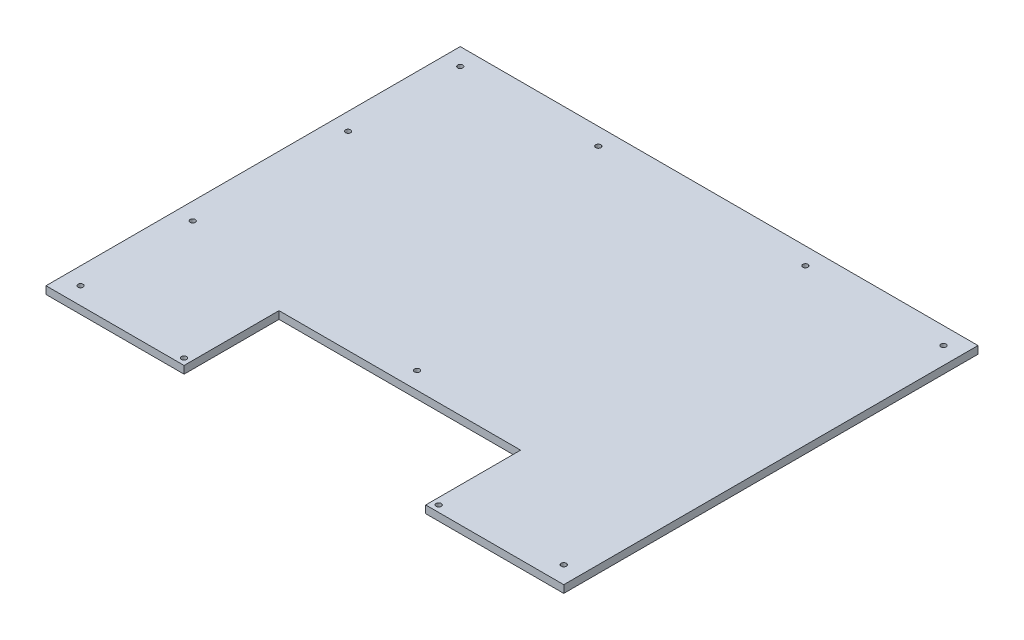
SolidWorks part; units mm, degrees
material "Polycarbonate"
ref_plane "Front Plane" through (0, 0, 0) normal (0, 0, 1) x (1, 0, 0)
ref_plane "Top Plane" through (0, 0, 0) normal (0, 1, 0) x (1, 0, 0)
ref_plane "Right Plane" through (0, 0, 0) normal (1, 0, 0) x (0, 0, -1)
sketch "Sketch1" plane through (0, 0, 0) normal (0, 1, 0) x (1, 0, 0)
  line L0 (0, 0) -> (0, -152.4) construction
  line L1 (-190.5, -152.4) -> (-88.9, -152.4)
  line L2 (-190.5, -152.4) -> (-190.5, 152.4)
  line L3 (-190.5, 152.4) -> (190.5, 152.4)
  line L4 (190.5, -152.4) -> (190.5, 152.4)
  line L5 (-190.5, -152.4) -> (190.5, 152.4) construction
  line L6 (-190.5, 152.4) -> (190.5, -152.4) construction
  line L8 (-88.9, -152.4) -> (-88.9, -82.55)
  line L9 (-88.9, -82.55) -> (88.9, -82.55)
  line L10 (88.9, -152.4) -> (88.9, -82.55)
  line L11 (88.9, -152.4) -> (190.5, -152.4)
  point P0 (0, 0)
  dimension "D1" = 304.8
  dimension "D2" = 381
  dimension "D3" = 69.85
  dimension "D4" = 177.8
extrude "Boss-Extrude1" add sketch "Sketch1" along normal blind 5.588
sketch "Sketch2" plane through (0, 5.588, 0) normal (0, 1, 0) x (1, 0, 0)
  line L0 (-177.8, 152.4) -> (-177.8, -152.4) construction
  line L1 (190.5, 152.4) -> (-190.5, 152.4) construction
  line L2 (-190.5, -152.4) -> (-88.9, -152.4) construction
  line L3 (-190.5, -139.7) -> (190.5, -139.7) construction
  line L4 (-190.5, 152.4) -> (-190.5, -152.4) construction
  line L5 (190.5, -152.4) -> (190.5, 152.4) construction
  line L6 (-190.5, 139.7) -> (190.5, 139.7) construction
  line L7 (177.8, 152.4) -> (177.8, -152.4) construction
  line L8 (-101.6, -152.4) -> (-101.6, -69.85) construction
  line L9 (-190.5, -152.4) -> (-88.9, -152.4) construction
  line L10 (-101.6, -69.85) -> (101.6, -69.85) construction
  line L11 (101.6, -69.85) -> (101.6, -152.4) construction
  line L12 (88.9, -152.4) -> (190.5, -152.4) construction
  line L13 (-88.9, -152.4) -> (-88.9, -82.55) construction
  line L14 (88.9, -82.55) -> (88.9, -152.4) construction
  line L15 (-88.9, -82.55) -> (88.9, -82.55) construction
  line L16 (177.8, 0) -> (-177.8, 0) construction
  line L17 (0, 139.7) -> (0, 0) construction
  line L18 (-93.6752, -139.7) -> (-93.6752, -147.6248) construction
  line L19 (-93.6752, -147.6248) -> (-101.6, -147.6248) construction
  line L20 (93.6752, -139.7) -> (93.6752, -147.6248) construction
  line L21 (93.6752, -147.6248) -> (101.6, -147.6248) construction
  point P20 (-177.8, -57.15)
  point P21 (-177.8, 57.15)
  point P22 (-76.2, 139.7)
  point P24 (76.2, 139.7)
  point P27 (-93.6752, -147.6248)
  point P38 (-88.9, -117.475)
  point P43 (0, -69.85)
  point P44 (-177.8, 139.7)
  point P45 (177.8, 139.7)
  point P46 (177.8, -139.7)
  point P47 (101.6, -139.7)
  point P48 (-101.6, -139.7)
  point P49 (-177.8, -139.7)
  point P56 (93.6752, -147.6248)
  dimension "D1" = 12.7
  dimension "D2" = 12.7
  dimension "D3" = 12.7
  dimension "D4" = 12.7
  dimension "D9" = 12.7
  dimension "D10" = 12.7
  dimension "D11" = 12.7
  dimension "D8" = 114.3
  dimension "D7" = 152.4
  dimension "D5" = 4.7752
  dimension "D6" = 4.7752
  dimension "D12" = 4.7752
hole_wizard "#6 Clearance Hole1" positions "3DSketch1" profile "Sketch3" hole size "#6" standard "ANSI Inch" end condition through all
sketch3d "3DSketch1"
  point P13 (-76.2, 5.588, -139.7)
  point P19 (76.2, 5.588, -139.7)
  point P43 (0, 5.588, 69.85)
  point P49 (-93.6752, 5.588, 147.6248)
  point P52 (-177.8, 5.588, 139.7)
  point P55 (-177.8, 5.588, -139.7)
  point P58 (177.8, 5.588, -139.7)
  point P61 (177.8, 5.588, 139.7)
  point P64 (93.6752, 5.588, 147.6248)
  point P74 (-177.8, 5.588, -57.15)
  point P77 (-177.8, 5.588, 57.15)
sketch "Sketch3" plane through (-76.2, 5.588, -139.7) normal (1, 0, 0) x (0, 0, 1)
  line L0 (0, 0) -> (0, 5.588)
  line L1 (0, 5.588) -> (1.8986, 5.588)
  line L2 (1.8986, 5.588) -> (1.8986, 0)
  line L5 (1.8986, 0) -> (0, 0)
  line L11 (0, -6.35) -> (0, 107.95) construction
  dimension "Thru Hole Dia." = 3.7973
  dimension "Thru Hole Depth" = 5.588
sketch "Sketch4" [suppressed] plane through (0, 3.175, 0) normal (0, 1, 0) x (1, 0, 0)
  line L1 (-114.3, -50.8) -> (-12.7, -50.8) construction
  line L2 (-114.3, -50.8) -> (-114.3, 25.4) construction
  line L3 (-114.3, 25.4) -> (-12.7, 25.4) construction
  line L4 (-12.7, -50.8) -> (-12.7, 25.4) construction
  line L5 (-190.5, 165.1) -> (-190.5, -165.1) construction
  line L6 (-88.9, -95.25) -> (88.9, -95.25) construction
  dimension "D1" = 76.2
  dimension "D2" = 44.45
  dimension "D3" = 101.6
  dimension "D4" = 76.2
hole_wizard "#6 Clearance Hole2" [suppressed] positions "3DSketch2" profile "Sketch5" hole size "#6" standard "ANSI Inch"
sketch3d "3DSketch2"
  point P0 (-114.3, 3.175, -25.4)
  point P3 (-12.7, 3.175, -25.4)
  point P6 (-12.7, 3.175, 50.8)
  point P9 (-114.3, 3.175, 50.8)
sketch "Sketch5" plane through (-114.3, 3.175, -25.4) normal (1, 0, 0) x (0, 0, 1)
  line L0 (0, 0) -> (0, 3.175)
  line L1 (0, 3.175) -> (1.8986, 3.175)
  line L2 (1.8986, 3.175) -> (1.8986, 0)
  line L5 (1.8986, 0) -> (0, 0)
  line L11 (0, -6.35) -> (0, 107.95) construction
  dimension "Thru Hole Dia." = 3.7973
  dimension "Thru Hole Depth" = 3.175
equation "\"D3@Sketch2\"=\"D1@Sketch2\""
equation "\"D4@Sketch2\"=\"D2@Sketch2\""
equation "\"D9@Sketch2\"=\"D1@Sketch2\""
equation "\"D10@Sketch2\"=\"D1@Sketch2\""
equation "\"D11@Sketch2\"=\"D1@Sketch2\""
equation "\"D2@Sketch2\"=\"D1@Sketch2\""
equation "\"D6@Sketch2\"=\"D5@Sketch2\""
equation "\"D12@Sketch2\"=\"D5@Sketch2\""
